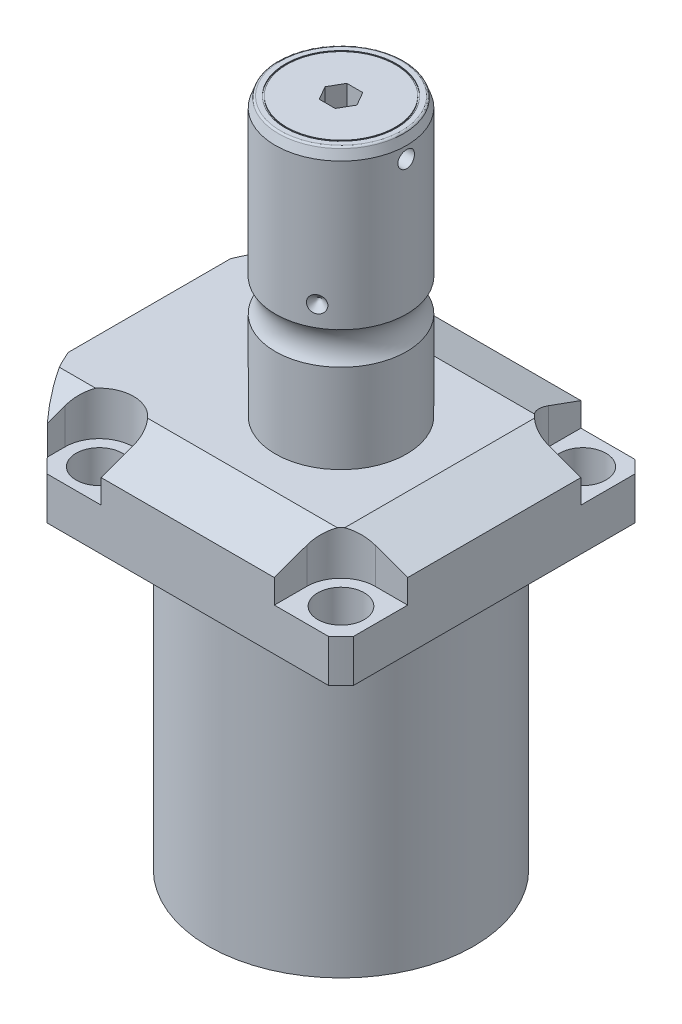
SolidWorks part; units mm, degrees
material "Alloy Steel"
ref_plane "Front Plane" through (0, 0, 0) normal (0, 0, 1) x (1, 0, 0)
ref_plane "Top Plane" through (0, 0, 0) normal (0, 1, 0) x (1, 0, 0)
ref_plane "Right Plane" through (0, 0, 0) normal (1, 0, 0) x (0, 0, -1)
ref_plane "Plane1" through (0, 0, 0) normal (0, 1, 0) x (0, 0, 1)
sketch "Sketch1" plane through (0, 0, 0) normal (0, 1, 0) x (0, 0, 1)
  line L0 (-44.45, 44.45) -> (44.45, 44.45)
  line L1 (44.45, 44.45) -> (44.45, -55.5498)
  line L2 (44.45, -55.5498) -> (-44.45, -55.5498)
  line L3 (-44.45, -55.5498) -> (-44.45, 44.45)
  line L4 (0, 0) -> (0, -60.6467) construction
  dimension "D1" = 55.5498
  dimension "D2" = 99.9998
  dimension "D3" = 88.9
extrude "Extrude1" add sketch "Sketch1" along normal blind 113.919
sketch "Sketch2" plane through (0, 0, 0) normal (0, -1, 0) x (1, 0, 0)
  circle A0 centre (0, 0) radius 60.325
  dimension "D1" = 120.65
extrude "Cut-Extrude1" cut sketch "Sketch2" against normal through all flip side to cut
ref_plane "Plane2" through (0, 0, 0) normal (1, 0, 0) x (0, 0, 1)
sketch "Sketch3" plane through (0, 0, 0) normal (1, 0, 0) x (0, 0, 1)
  line L0 (38.4937, 0) -> (38.4937, -88.9)
  line L1 (38.4937, -88.9) -> (76.5937, -88.9)
  line L2 (76.5937, -88.9) -> (76.5937, 0)
  line L3 (76.5937, 0) -> (38.4937, 0)
  line L4 (0, -93.345) -> (0, 4.445) construction
  line L5 (40.7836, 0) -> (-40.7836, 0) construction
  dimension "D1" = 76.9874
  dimension "D2" = 153.1874
  dimension "D3" = 88.9
revolve "Cut-Revolve1" cut sketch "Sketch3" angle 360 about L4
fillet "Fillet1" radius 0.381 1 edges at (0, 88.9, 38.4937)
sketch "Sketch4" plane through (0, 113.919, 0) normal (0, 1, 0) x (-1, 0, 0)
  line L0 (-44.45, 40.7836) -> (-44.45, -40.7836) construction
  line L1 (40.7836, 44.45) -> (-40.7836, 44.45) construction
  line L2 (-25.1206, -44.45) -> (-25.1206, -35.052)
  line L3 (-44.45, -44.45) -> (-25.1206, -44.45)
  line L4 (-44.45, -25.1206) -> (-44.45, -44.45)
  line L5 (-35.052, -25.1206) -> (-44.45, -25.1206)
  line L6 (44.9834, -44.45) -> (25.1206, -44.45)
  line L7 (25.1206, 44.45) -> (25.1206, 35.052)
  line L8 (44.9834, 44.45) -> (44.9834, 35.052)
  line L9 (44.9834, 44.45) -> (25.1206, 44.45)
  line L10 (-35.052, 25.1206) -> (-44.45, 25.1206)
  line L11 (-44.45, 25.1206) -> (-44.45, 44.45)
  line L12 (-44.45, 44.45) -> (-25.1206, 44.45)
  line L13 (-25.1206, 44.45) -> (-25.1206, 35.052)
  line L14 (-48.9217, 0) -> (49.4551, 0) construction
  line L15 (44.9834, -44.45) -> (44.9834, -35.052)
  line L16 (25.1206, -44.45) -> (25.1206, -35.052)
  arc A0 (25.1206, -35.052) -> (44.9834, -35.052) centre (35.052, -35.052) cw
  arc A1 (-35.052, -25.1206) -> (-25.1206, -35.052) centre (-35.052, -35.052) cw
  arc A2 (-35.052, 25.1206) -> (-25.1206, 35.052) centre (-35.052, 35.052) ccw
  arc A3 (25.1206, 35.052) -> (44.9834, 35.052) centre (35.052, 35.052) ccw
  dimension "D2" = 9.9314
  dimension "D1" = 35.052
  dimension "D3" = 35.052
  dimension "D4" = 35.052
extrude "Cut-Extrude2" cut sketch "Sketch4" against normal blind 12.7
ref_plane "Plane3" through (0, 0, 0) normal (1, 0, 0) x (0, 0, -1)
sketch "Sketch5" plane through (0, 0, 0) normal (1, 0, 0) x (0, 0, -1)
  line L0 (-28.575, 113.919) -> (-44.45, 108.141)
  line L1 (0, 0) -> (0, 154.1081) construction
  line L2 (-28.575, 113.919) -> (-44.45, 113.919)
  line L3 (-44.45, 113.919) -> (-44.45, 108.141)
  dimension "D1" = 15.875
  dimension "D2" = 20
extrude "Cut-Extrude9" cut sketch "Sketch5" against normal through all and the other way through all
mirror "Mirror1" about plane through (0, 0, 0) normal (0, 0, 1) of "Cut-Extrude9"
ref_plane "Plane7" through (0, 0, 0) normal (0, 0, 1) x (1, 0, 0)
sketch "Sketch9" plane through (0, 0, 0) normal (0, 0, 1) x (1, 0, 0)
  line L0 (28.575, 113.919) -> (44.45, 108.141)
  line L1 (44.45, 108.141) -> (44.45, 113.919)
  line L2 (44.45, 113.919) -> (28.575, 113.919)
  dimension "D1" = 15.875
  dimension "D2" = 20
extrude "Cut-Extrude7" cut sketch "Sketch9" against normal through all and the other way through all
ref_plane "Plane8" through (-41.402, 88.9, -18.1102) normal (1, 0, 0) x (0, 1, 0)
sketch "Sketch20" plane through (-41.402, 88.9, -18.1102) normal (1, 0, 0) x (0, 1, 0)
  line L0 (-88.9, 18.1102) -> (39.8401, 18.1102) construction
  line L1 (-7.2797, 36.2204) -> (36.9042, 36.2204) construction
  line L2 (0, 41.9227) -> (1.4478, 41.9227)
  line L3 (0, 58.8938) -> (0, -22.6734) construction
  line L4 (1.4478, 41.9227) -> (1.4478, 39.4716)
  line L5 (1.4478, 39.4716) -> (2.4638, 39.4716)
  line L6 (2.4638, 39.4716) -> (2.4638, 37.465)
  line L7 (2.4638, 37.465) -> (13.4366, 37.465)
  line L8 (13.4366, 37.465) -> (13.4366, 36.2204)
  line L9 (13.4366, 36.2204) -> (0, 36.2204)
  line L10 (0, 41.9227) -> (0, 36.2204)
  dimension "D1" = 18.1102
  dimension "D2" = 11.4046
  dimension "D3" = 1.4478
  dimension "D4" = 6.5024
  dimension "D5" = 1.016
  dimension "D6" = 2.4892
  dimension "D7" = 10.9728
revolve "Cut-Revolve4" cut sketch "Sketch20" angle 360 about L1
mirror "Mirror10" about plane through (0, 0, 0) normal (0, 0, 1) of "Cut-Revolve4"
sketch "Sketch10" plane through (-41.402, 88.9, -18.1102) normal (1, 0, 0) x (0, 1, 0)
  line L0 (-1.0325, 0) -> (1.5659, 0) construction
  line L1 (13.4366, 1.2446) -> (2.4638, 1.2446) construction
  line L2 (2.4638, -1.2446) -> (13.4366, -1.2446) construction
  line L3 (0, 58.8938) -> (0, -22.6734) construction
  circle A0 centre (0.2667, 4.5212) radius 1.1811
  dimension "D1" = 2.3622
  dimension "D2" = 0.2667
  dimension "D3" = 9.0424
revolve "Revolve4" add sketch "Sketch10" angle 360 about L0
ref_plane "Plane9" through (-41.402, 88.9, 18.1102) normal (1, 0, 0) x (0, 1, 0)
sketch "Sketch11" plane through (-41.402, 88.9, 18.1102) normal (1, 0, 0) x (0, 1, 0)
  line L0 (-1.0325, 0) -> (1.5659, 0) construction
  line L1 (13.4366, 1.2446) -> (2.4638, 1.2446) construction
  line L3 (0, 22.6734) -> (0, -58.8938) construction
  line L4 (2.4638, -1.2446) -> (13.4366, -1.2446) construction
  circle A0 centre (0.2667, 4.5212) radius 1.1811
  point P10 (0, 0)
  dimension "D1" = 2.3622
  dimension "D2" = 9.0424
  dimension "D3" = 0.2667
revolve "Revolve2" add sketch "Sketch11" angle 360 about L0
ref_plane "Plane10" through (-55.5498, 101.9048, 12.9794) normal (0, 0, 1) x (0, 1, 0)
sketch "S2D0007" plane through (-55.5498, 101.9048, 12.9794) normal (0, 0, 1) x (0, 1, 0)
  line L0 (0, 0) -> (10.4775, 0)
  line L1 (10.4775, 0) -> (10.4775, -0.254)
  line L2 (10.4775, -0.254) -> (6.1849, -0.254)
  line L3 (6.1849, -0.254) -> (5.6423, -2.8067)
  line L4 (5.6423, -2.8067) -> (4.9784, -3.4706)
  line L5 (4.9784, -3.4706) -> (4.9784, -14.224)
  line L6 (4.9784, -14.224) -> (0, -14.224)
  line L7 (0, -14.224) -> (0, 0)
  line L8 (0, -14.9352) -> (0, 0.7112) construction
  line L9 (-13.0048, 0) -> (-13.0048, -14.7662) construction
  dimension "D1" = 0.254
  dimension "D2" = 13.0048
revolve "Cut-Revolve2" cut sketch "S2D0007" angle 360 about L8
ref_plane "Plane11" through (-55.5498, 101.9048, -12.9794) normal (0, 0, 1) x (0, 1, 0)
sketch "Sketch13" plane through (-55.5498, 101.9048, -12.9794) normal (0, 0, 1) x (0, 1, 0)
  line L0 (0, 0) -> (10.4775, 0)
  line L1 (10.4775, 0) -> (10.4775, -0.254)
  line L2 (10.4775, -0.254) -> (6.1849, -0.254)
  line L3 (6.1849, -0.254) -> (5.6423, -2.8067)
  line L4 (5.6423, -2.8067) -> (4.9784, -3.4706)
  line L5 (4.9784, -3.4706) -> (4.9784, -14.224)
  line L6 (4.9784, -14.224) -> (0, -14.224)
  line L7 (0, -14.224) -> (0, 0)
  line L8 (0, -14.9352) -> (0, 0.7112) construction
  line L9 (-13.0048, 0) -> (-13.0048, -14.7662) construction
  dimension "D1" = 0.254
  dimension "D2" = 13.0048
revolve "Cut-Revolve3" cut sketch "Sketch13" angle 360 about L8
sketch "Sketch14" plane through (-55.2958, 0, 0) normal (-1, 0, 0) x (0, 0, 1)
  circle A0 centre (-12.9794, 101.9048) radius 7.112
  circle A1 centre (-12.9794, 101.9048) radius 4.9784 construction
  dimension "D1" = 14.224
extrude "Extrude2" add sketch "Sketch14" along normal blind 1.27
ref_plane "Plane12" through (0, 0, 0) normal (1, 0, 0) x (0, -1, 0)
sketch "Sketch15" plane through (0, 0, 0) normal (1, 0, 0) x (0, -1, 0)
  line L0 (-113.919, 0) -> (-113.919, 19.05)
  line L1 (-113.919, 19.05) -> (-139.6411, 19.05)
  line L2 (-149.0553, 19.05) -> (-191.4144, 19.05)
  line L3 (-194.3354, 17.9868) -> (-194.3354, 0)
  line L4 (-194.3354, 0) -> (-113.919, 0)
  line L5 (-197.6361, 0) -> (-64.6704, 0) construction
  line L6 (-113.919, 27.5233) -> (-113.919, -27.5233) construction
  line L7 (-88.9, 40.7836) -> (-88.9, 44.45) construction
  line L8 (-191.4144, 19.05) -> (-194.3354, 17.9868)
  arc A0 (-149.0553, 19.05) -> (-139.6411, 19.05) centre (-144.3482, 25.4254) ccw
  dimension "D2" = 20
  dimension "D4" = 7.9248
  dimension "D6" = 35.0012
  dimension "D1" = 105.4354
  dimension "D3" = 38.1
  dimension "D5" = 49.9872
  dimension "D7" = 2.921
revolve "Revolve3" add sketch "Sketch15" angle 360 about L5
ref_plane "Plane13" through (0, 0, 0) normal (0, 0, -1) x (0, -1, 0)
hole_wizard "Hole1" positions "Sketch18" profile "Sketch17" legacy end condition up to next
sketch "Sketch18" plane through (0, 101.219, 0) normal (0, 1, 0) x (-1, 0, 0)
  arc A0 (44.9834, -35.052) -> (25.1206, -35.052) centre (35.052, -35.052) ccw construction
  arc A1 (25.1206, 35.052) -> (44.9834, 35.052) centre (35.052, 35.052) ccw construction
  arc A2 (-35.052, 25.1206) -> (-25.1206, 35.052) centre (-35.052, 35.052) ccw construction
  arc A3 (-25.1206, -35.052) -> (-35.052, -25.1206) centre (-35.052, -35.052) ccw construction
  point P0 (-35.052, -35.052)
  point P1 (-35.052, 35.052)
  point P3 (35.052, 35.052)
  point P5 (35.052, -35.052)
sketch "Sketch17" plane through (35.052, 101.219, -35.052) normal (1, 0, 0) x (0, 0, 1)
  line L0 (0, 0) -> (0, 12.319)
  line L1 (0, 12.319) -> (6.7437, 12.319)
  line L2 (6.7437, 12.319) -> (6.7437, 0)
  line L3 (6.7437, 0) -> (0, 0)
  line L4 (0, 110) -> (0, -10) construction
  dimension "Diameter" = 13.4874
  dimension "Depth" = 12.319
chamfer "Chamfer1" distance 0.635 angle 45 2 edges at (-41.402, 91.3638, 16.8656) (-41.402, 91.3638, -16.8656)
fillet "Fillet2" radius 0.635 1 edges at (0, 194.3354, 17.9868)
sketch "Sketch21" plane through (0, 194.3354, 0) normal (0, 1, 0) x (1, 0, 0)
  circle A0 centre (0, 0) radius 16.129
  circle A1 centre (0, 0) radius 15.748
  dimension "D1" = 31.496
  dimension "D2" = 32.258
extrude "Cut-Extrude10" cut sketch "Sketch21" against normal blind 0.254
sketch "Sketch22" plane through (0, 194.3354, 0) normal (0, 1, 0) x (1, 0, 0)
  line L1 (4.6188, 0) -> (2.3094, 4)
  line L2 (2.3094, 4) -> (-2.3094, 4)
  line L3 (-2.3094, 4) -> (-4.6188, 0)
  line L4 (-4.6188, 0) -> (-2.3094, -4)
  line L5 (-2.3094, -4) -> (2.3094, -4)
  line L6 (2.3094, -4) -> (4.6188, 0)
  circle A0 centre (0, 0) radius 4 construction
  dimension "D1" = 8
extrude "Cut-Extrude11" cut sketch "Sketch22" against normal blind 7.9756
sketch "Sketch23" plane through (0, 0, 0) normal (0, 0, 1) x (1, 0, 0)
  line L0 (7.8373, 155.0162) -> (-56.125, 155.0162) construction
  line L1 (-19.05, 157.4292) -> (-16.637, 155.0162)
  line L3 (-19.05, 191.4144) -> (-19.05, 149.0553) construction
  line L4 (-16.637, 155.0162) -> (-19.05, 155.0162)
  line L5 (-19.05, 155.0162) -> (-19.05, 157.4292)
  arc A0 (19.05, 149.0553) -> (19.05, 139.6411) centre (25.4254, 144.3482) ccw construction
  dimension "D3" = 10.668
  dimension "D1" = 4.826
  dimension "D2" = 45
revolve "Cut-Revolve5" cut sketch "Sketch23" angle 360 about L0
pattern_circular "CirPattern1" count 3 over 360 about axis through (0, 197.6361, 0) along (0, 1, 0) of "Cut-Revolve5"
sketch "Sketch24" plane through (0, 0, 0) normal (0, 0, 1) x (1, 0, 0)
  line L0 (3.2512, 187.9854) -> (47.4739, 187.9854) construction
  line L2 (19.05, 190.3984) -> (15.24, 190.3984)
  line L3 (19.05, 190.3984) -> (19.05, 187.9854)
  line L4 (19.05, 187.9854) -> (15.24, 187.9854)
  line L5 (15.24, 190.3984) -> (15.24, 187.9854)
  line L6 (17.5422, 194.3354) -> (-17.5422, 194.3354) construction
  line L7 (19.05, 149.0553) -> (19.05, 191.4144) construction
  dimension "D1" = 3.81
  dimension "D2" = 4.826
  dimension "D3" = 6.35
revolve "Cut-Revolve6" cut sketch "Sketch24" angle 360 about L0
